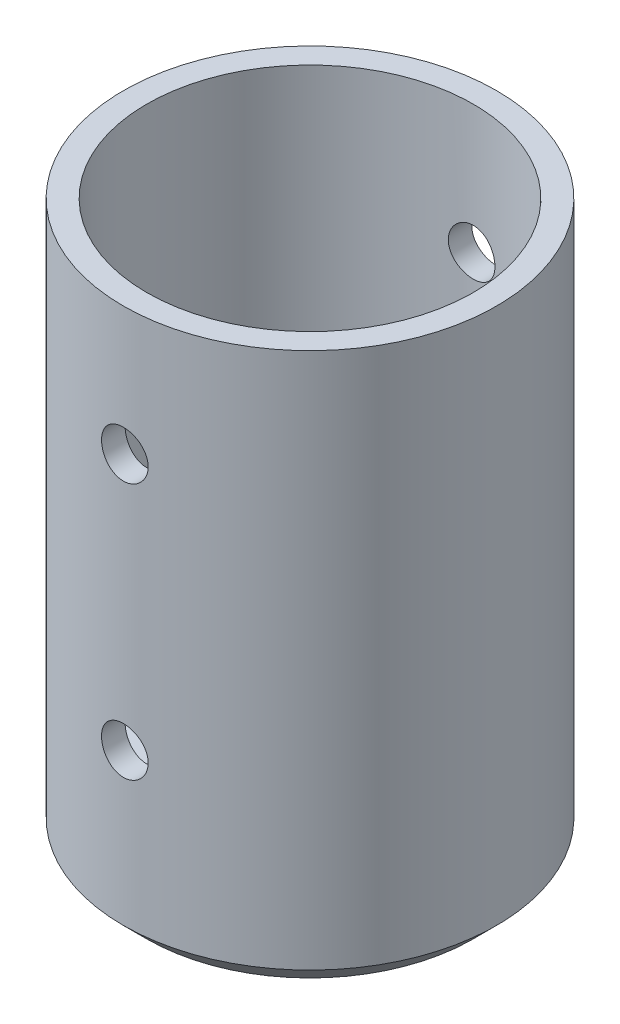
SolidWorks part; units mm, degrees
ref_plane "Front Plane" through (0, 0, 0) normal (0, 0, 1) x (1, 0, 0)
ref_plane "Top Plane" through (0, 0, 0) normal (0, 1, 0) x (1, 0, 0)
ref_plane "Right Plane" through (0, 0, 0) normal (1, 0, 0) x (0, 0, -1)
sketch "Sketch1" plane through (0, 0, 0) normal (0, 1, 0) x (1, 0, 0)
  circle A0 centre (0, 0) radius 25.4
  dimension "D1" = 50.8
extrude "Boss-Extrude1" add sketch "Sketch1" along normal blind 76.2
sketch "Sketch2" plane through (0, 76.2, 0) normal (0, 1, 0) x (1, 0, 0)
  circle A0 centre (0, 0) radius 22.225
  dimension "D1" = 44.45
extrude "Cut-Extrude1" cut sketch "Sketch2" against normal blind 69.85
chamfer "Chamfer1" distance 3.175 angle 45 1 edges at (0, 0, 25.4)
sketch "Sketch3" plane through (0, 6.35, 0) normal (0, 1, 0) x (1, 0, 0)
  line L0 (-25.4, 0) -> (25.4, 0) construction
  circle A0 centre (-12.7, 0) radius 1.5875
  circle A1 centre (12.7, 0) radius 1.5875
  circle A2 centre (0, 0) radius 25.4 construction
  dimension "D3" = 3.175
  dimension "D4" = 3.175
  dimension "D1" = 12.7
  dimension "D2" = 12.7
extrude "Cut-Extrude2" cut sketch "Sketch3" against normal blind 63.5
sketch "Sketch5" plane through (0, 0, 0) normal (0, -1, 0) x (1, 0, 0)
  line L0 (0, 0) -> (0, 25.4) construction
  dimension "D1" = 25.4
ref_plane "Plane1" through (0, 0, 25.4) normal (0, 0, 1) x (1, 0, 0)
sketch "Sketch6" plane through (0, 0, 25.4) normal (0, 0, 1) x (1, 0, 0)
  line L0 (-38.5638, 6.35) -> (39.7374, 6.35) construction
  line L2 (-22.225, 0) -> (22.225, 0) construction
  line L3 (-41.8054, 41.275) -> (42.2525, 41.275) construction
  circle A0 centre (0, 23.8125) radius 3.175
  circle A1 centre (0, 58.7375) radius 3.175
  dimension "D4" = 6.35
  dimension "D1" = 6.35
  dimension "D2" = 34.925
  dimension "D3" = 17.4625
extrude "Cut-Extrude3" cut sketch "Sketch6" against normal through all
